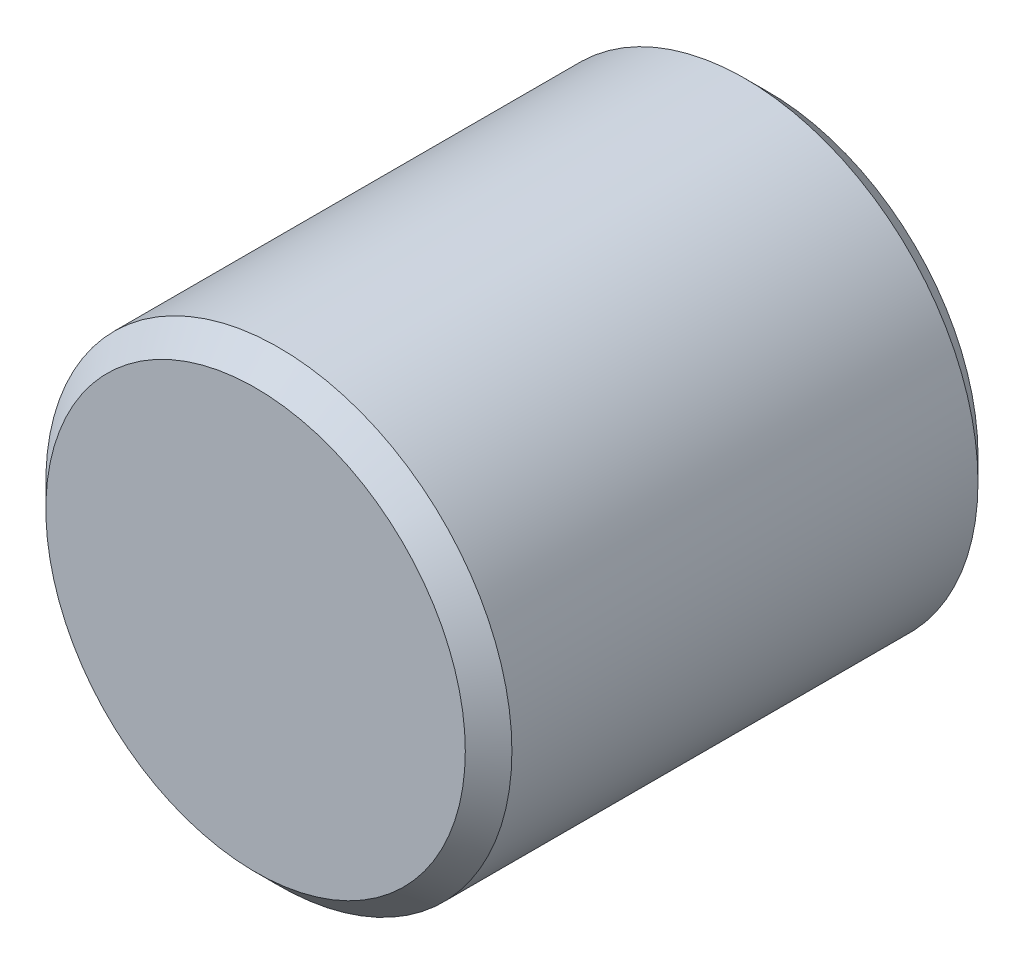
SolidWorks part; units mm, degrees
ref_plane "Front Plane" through (0, 0, 0) normal (0, 0, 1) x (1, 0, 0)
ref_plane "Top Plane" through (0, 0, 0) normal (0, 1, 0) x (1, 0, 0)
ref_plane "Right Plane" through (0, 0, 0) normal (1, 0, 0) x (0, 0, -1)
sketch "Sketch1" plane through (0, 0, 0) normal (0, 0, 1) x (1, 0, 0)
  circle A0 centre (0, 0) radius 5
  dimension "D1" = 10
extrude "Boss-Extrude1" add sketch "Sketch1" along normal blind 11
hole_wizard "M3 Tapped Hole1" positions "Sketch4" profile "Sketch5" tap size "M3" standard "DIN"
sketch "Sketch4" plane through (0, 0, 0) normal (0, 0, -1) x (-1, 0, 0)
  point P0 (0, 0)
sketch "Sketch5" plane through (0, 0, 0) normal (1, 0, 0) x (0, 1, 0)
  line L0 (0, 0) -> (0, 8.2511)
  line L1 (0, 8.2511) -> (1.25, 7.5)
  line L2 (1.25, 7.5) -> (1.25, 0)
  line L5 (1.25, 0) -> (0, 0)
  line L10 (0, 8.2511) -> (-1.25, 7.5) construction
  line L11 (0, -6.35) -> (0, 107.95) construction
  dimension "Tap Drill Dia." = 2.5
  dimension "Tap Drill Depth" = 7.5
  dimension "Drill Angle" = 118
cosmetic thread "Hole Thread1" parameters "D1"=5, "D2"=3
chamfer "Chamfer2" distance 0.5 angle 45 2 edges at (5, 0, 0) (5, 0, 11)
